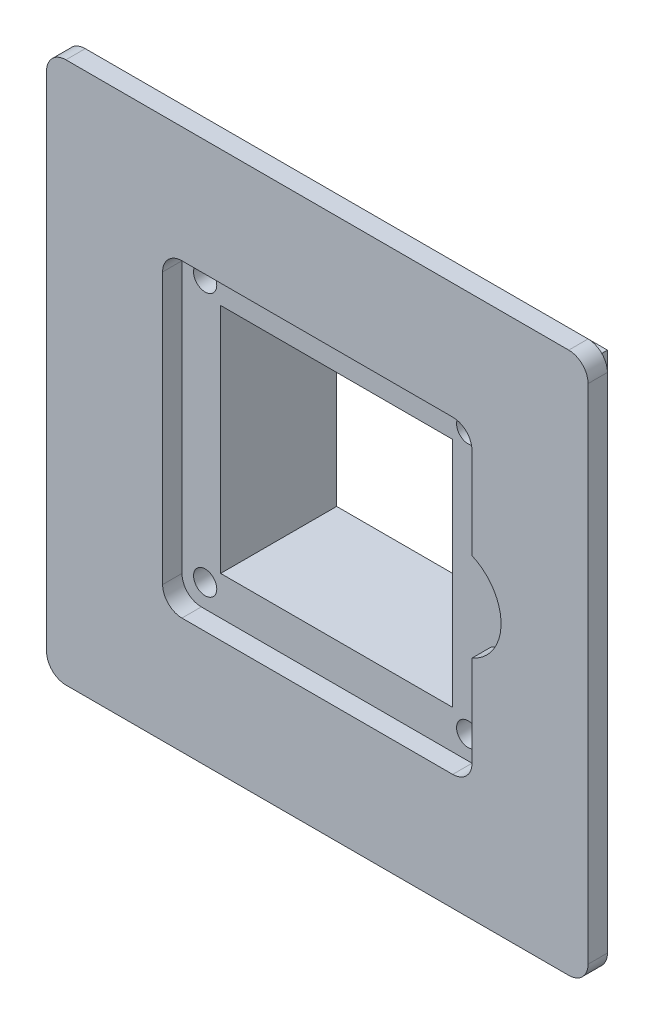
SolidWorks part; units mm, degrees
ref_plane "Front Plane" through (0, 0, 0) normal (0, 0, 1) x (1, 0, 0)
ref_plane "Top Plane" through (0, 0, 0) normal (0, 1, 0) x (1, 0, 0)
ref_plane "Right Plane" through (0, 0, 0) normal (1, 0, 0) x (0, 0, -1)
sketch "Sketch1" plane through (0, 0, 0) normal (0, 0, 1) x (1, 0, 0)
  line L1 (0, 0) -> (70, 0)
  line L2 (0, 0) -> (0, 70)
  line L3 (0, 70) -> (70, 70)
  line L4 (70, 0) -> (70, 70)
  dimension "D1" = 70
  dimension "D2" = 70
extrude "Boss-Extrude1" add sketch "Sketch1" along normal blind 2.5
sketch "Sketch2" plane through (0, 0, 2.5) normal (0, 0, 1) x (1, 0, 0)
  line L4 (70, 70) -> (0, 70) construction
  line L5 (15, 55) -> (55, 55)
  line L6 (15, 55) -> (15, 15)
  line L7 (15, 15) -> (55, 15)
  line L8 (55, 55) -> (55, 15)
  line L9 (0, 70) -> (0, 0) construction
  dimension "D2" = 15
  dimension "D3" = 15
  dimension "D13" = 40
  dimension "D14" = 40
sketch "Sketch3" plane through (0, 0, 0) normal (0, 0, -1) x (-1, 0, 0)
  line L1 (-60, 60) -> (-10, 60)
  line L2 (-60, 60) -> (-60, 10)
  line L3 (-60, 10) -> (-10, 10)
  line L4 (-10, 60) -> (-10, 10)
  line L6 (-35, 70) -> (-35, 0) construction
  line L7 (-70, 70) -> (0, 70) construction
  line L8 (0, 0) -> (-70, 0) construction
  line L9 (-70, 35) -> (0, 35) construction
  line L10 (-70, 0) -> (-70, 70) construction
  line L11 (0, 70) -> (0, 0) construction
  dimension "D1" = 50
  dimension "D2" = 50
  dimension "D3" = 25
  dimension "D4" = 25
extrude "Boss-Extrude4" add sketch "Sketch3" along normal blind 10
sketch "Sketch5" plane through (0, 0, -10) normal (0, 0, -1) x (-1, 0, 0)
  line L0 (-10, 60) -> (-60, 60) construction
  line L1 (-55, 15) -> (-15, 15)
  line L2 (-55, 15) -> (-55, 55)
  line L3 (-55, 55) -> (-15, 55)
  line L4 (-15, 15) -> (-15, 55)
  line L5 (-10, 10) -> (-10, 60) construction
  dimension "D1" = 40
  dimension "D2" = 40
  dimension "D3" = 5
  dimension "D4" = 5
extrude "Boss-Extrude5" add sketch "Sketch5" along normal blind 5
extrude "Cut-Extrude4" cut sketch "Sketch2" against normal blind 2.5
sketch "Sketch6" plane through (0, 0, 0) normal (0, 0, 1) x (1, 0, 0)
  line L0 (15, 55) -> (15, 15) construction
  line L1 (20, 20) -> (50, 20)
  line L2 (20, 20) -> (20, 50)
  line L3 (20, 50) -> (50, 50)
  line L4 (50, 20) -> (50, 50)
  line L5 (55, 55) -> (15, 55) construction
  dimension "D1" = 30
  dimension "D2" = 30
  dimension "D3" = 5
  dimension "D4" = 5
extrude "Cut-Extrude5" cut sketch "Sketch6" against normal up to surface (15 mm away) up to face at (35, 35, -15)
sketch "Sketch8" plane through (0, 0, 0) normal (0, 0, 1) x (1, 0, 0)
  line L0 (55, 15) -> (55, 55) construction
  line L1 (55, 55) -> (15, 55) construction
  line L2 (15, 55) -> (15, 15) construction
  line L3 (15, 15) -> (55, 15) construction
  line L4 (15, 55) -> (15, 15) construction
  line L6 (55, 15) -> (55, 55) construction
  circle A0 centre (52, 52) radius 1.5
  circle A1 centre (52, 18) radius 1.5
  circle A2 centre (18, 52) radius 1.5
  circle A3 centre (18, 18) radius 1.5
  dimension "D1" = 3
  dimension "D4" = 3
  dimension "D5" = 3
  dimension "D6" = 3
  dimension "D2" = 3
  dimension "D3" = 3
  dimension "D7" = 3
  dimension "D8" = 3
  dimension "D9" = 3
  dimension "D10" = 3
  dimension "D11" = 3
  dimension "D12" = 3
extrude "Cut-Extrude6" cut sketch "Sketch8" against normal blind 5
sketch "Sketch9" plane through (0, 0, -15) normal (0, 0, -1) x (-1, 0, 0)
  line L0 (-15, 15) -> (-15, 55) construction
  line L1 (-55, 15) -> (-15, 15) construction
  line L2 (-15, 55) -> (-55, 55) construction
  line L3 (-55, 55) -> (-55, 15) construction
  circle A0 centre (-18, 18) radius 1.5
  circle A1 centre (-52, 18) radius 1.5
  circle A2 centre (-18, 52) radius 1.5
  circle A3 centre (-52, 52) radius 1.5
  dimension "D1" = 3
  dimension "D3" = 3
  dimension "D4" = 3
  dimension "D5" = 3
  dimension "D6" = 3
  dimension "D2" = 3
  dimension "D7" = 3
  dimension "D8" = 3
  dimension "D9" = 3
  dimension "D10" = 3
  dimension "D11" = 3
  dimension "D12" = 3
extrude "Cut-Extrude7" cut sketch "Sketch9" against normal blind 5
fillet "Fillet1" radius 2.5 4 edges at (0, 0, 1.25) (70, 0, 1.25) (0, 70, 1.25) (70, 70, 1.25)
fillet "Fillet2" radius 2.5 2 edges at (15, 55, 1.25) (55, 55, 1.25)
fillet "Fillet3" radius 2.5 2 edges at (15, 15, 1.25) (55, 15, 1.25)
sketch "Sketch10" plane through (0, 0, 2.5) normal (0, 0, 1) x (1, 0, 0)
  line L4 (55, 17.5) -> (55, 52.5) construction
  line L5 (2.5, 0) -> (67.5, 0) construction
  line L6 (67.5, 70) -> (2.5, 70) construction
  circle A1 centre (52.5, 35) radius 6.25
  dimension "D1" = 2.5
  dimension "D2" = 12.5
  dimension "D3" = 35
  dimension "D4" = 35
extrude "Cut-Extrude12" cut sketch "Sketch10" against normal blind 2.5
